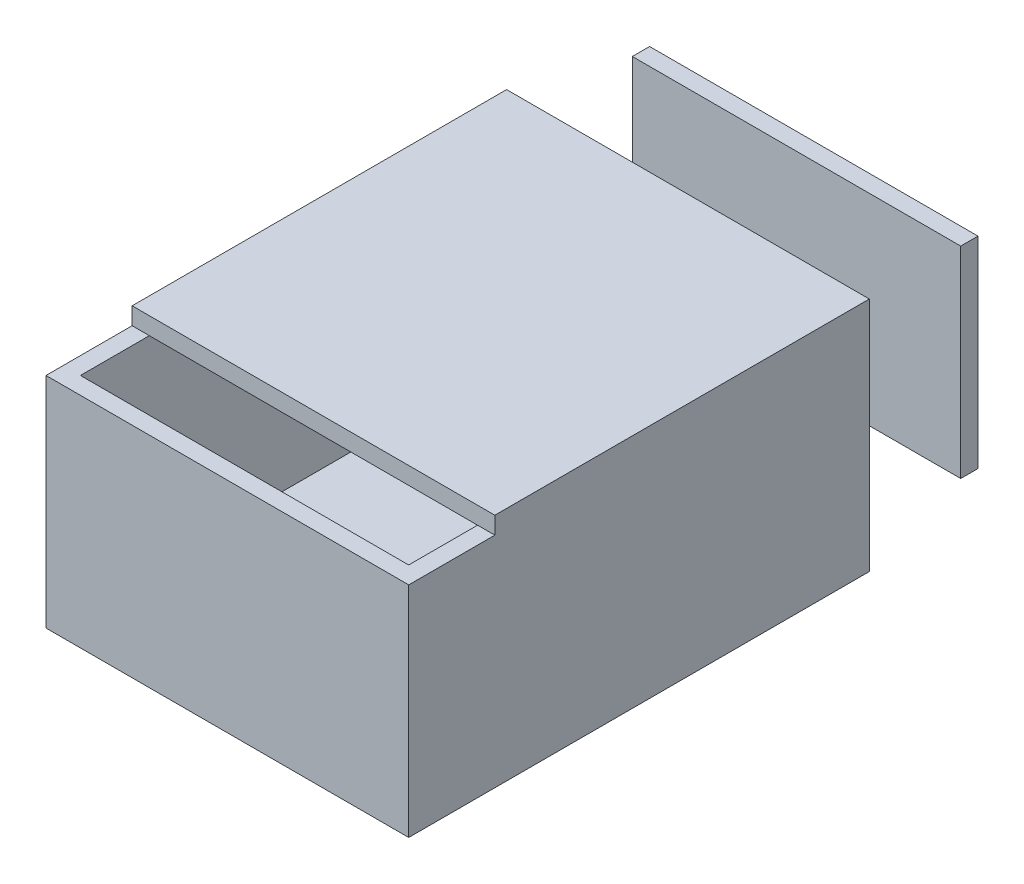
SolidWorks part; units mm, degrees
ref_plane "Plano frontal" through (0, 0, 0) normal (0, 0, 1) x (1, 0, 0)
ref_plane "Plano superior" through (0, 0, 0) normal (0, 1, 0) x (1, 0, 0)
ref_plane "Plano direito" through (0, 0, 0) normal (1, 0, 0) x (0, 0, -1)
sketch "Esboço2" plane through (0, 0, 0) normal (0, 1, 0) x (1, 0, 0)
  line L0 (0, 0) -> (63, 0)
  line L1 (63, 0) -> (63, -80)
  line L2 (63, -80) -> (0, -80)
  line L3 (0, -80) -> (0, 0)
  dimension "D1" = 63
  dimension "D2" = 80
extrude "Ressalto-extrusão1" add sketch "Esboço2" along normal blind 3
sketch "Esboço3" plane through (0, 3, 0) normal (0, 1, 0) x (1, 0, 0)
  line L0 (63, -80) -> (63, 0)
  line L1 (63, 0) -> (60.0017, 0)
  line L2 (63, 0) -> (0, 0) construction
  line L3 (60.0017, 0) -> (60.0017, -77.0106)
  line L4 (60.0017, -77.0106) -> (2.9904, -77.0106)
  line L5 (2.9904, -77.0106) -> (2.9904, 0)
  line L6 (2.9904, 0) -> (0, 0)
  line L7 (0, 0) -> (0, -80)
  line L8 (0, -80) -> (63, -80)
extrude "Ressalto-extrusão2" add sketch "Esboço3" along normal blind 35
sketch "Esboço4" plane through (0, 38, 0) normal (0, 1, 0) x (1, 0, 0)
  line L0 (63, 0) -> (63, -65.0418)
  line L1 (63, -80) -> (63, 0) construction
  line L2 (63, -65.0418) -> (0, -65.0418)
  line L3 (0, 0) -> (0, -80) construction
  line L4 (0, -65.0418) -> (0, 0)
  line L5 (0, 0) -> (63, 0)
extrude "Ressalto-extrusão3" add sketch "Esboço4" along normal blind 3
ref_plane "Plano4" through (0, 0, -20) normal (0, 0, -1) x (-1, 0, 0)
sketch "Esboço6" plane through (0, 0, -20) normal (0, 0, -1) x (-1, 0, 0)
  line L0 (-58.875, 36.8983) -> (-58.875, 1.9308)
  line L1 (-58.875, 1.9308) -> (-1.8364, 1.9308)
  line L2 (-1.8364, 1.9308) -> (-1.8364, 36.8983)
  line L3 (-1.8364, 36.8983) -> (-58.875, 36.8983)
extrude "Ressalto-extrusão4" add sketch "Esboço6" along normal blind 3 separate body
